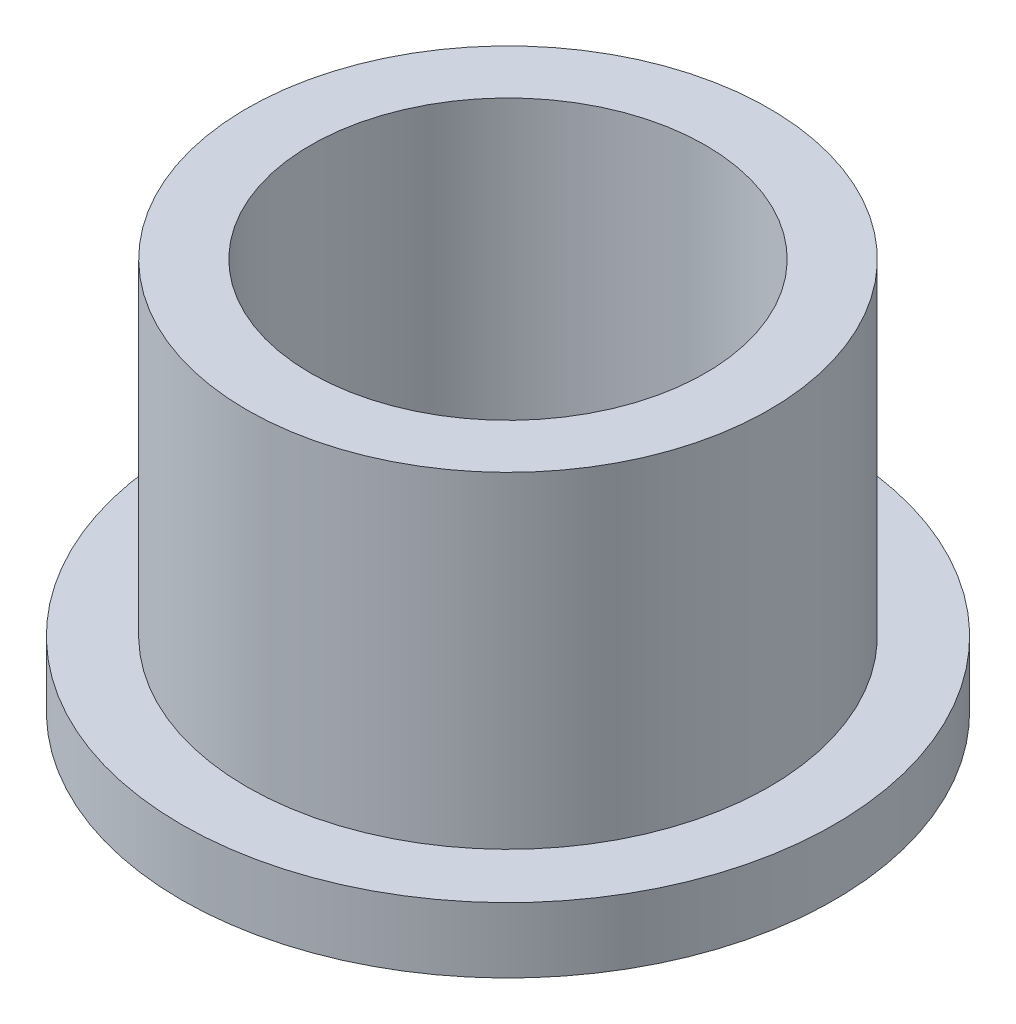
SolidWorks part; units mm, degrees
ref_plane "Front" through (0, 0, 0) normal (0, 0, 1) x (1, 0, 0)
ref_plane "Top" through (0, 0, 0) normal (0, 1, 0) x (1, 0, 0)
ref_plane "Right" through (0, 0, 0) normal (1, 0, 0) x (0, 0, -1)
sketch "Sketch1" plane through (0, 0, 0) normal (0, 1, 0) x (1, 0, 0)
  circle A0 centre (0, 0) radius 4.8006
  circle A1 centre (0, 0) radius 6.35
  circle A2 centre (0, 0) radius 7.9375
  dimension "ID" = 9.6012
  dimension "OD" = 12.7
  dimension "FlangeOD" = 15.875
sketch "Sketch2" plane through (0, 0, 0) normal (0, 1, 0) x (1, 0, 0)
  circle A0 centre (0, 0) radius 4.8006 construction
  circle A1 centre (0, 0) radius 6.35 construction
  circle A2 centre (0, 0) radius 4.8006
  circle A3 centre (0, 0) radius 6.35
extrude "Boss-Extrude1" add sketch "Sketch2" along normal blind 9.525
sketch "Sketch3" plane through (0, 0, 0) normal (0, 1, 0) x (1, 0, 0)
  circle A0 centre (0, 0) radius 7.9375 construction
  circle A1 centre (0, 0) radius 6.35 construction
  circle A2 centre (0, 0) radius 7.9375
  circle A3 centre (0, 0) radius 6.35
extrude "Boss-Extrude2" add sketch "Sketch3" along normal blind 1.5875
